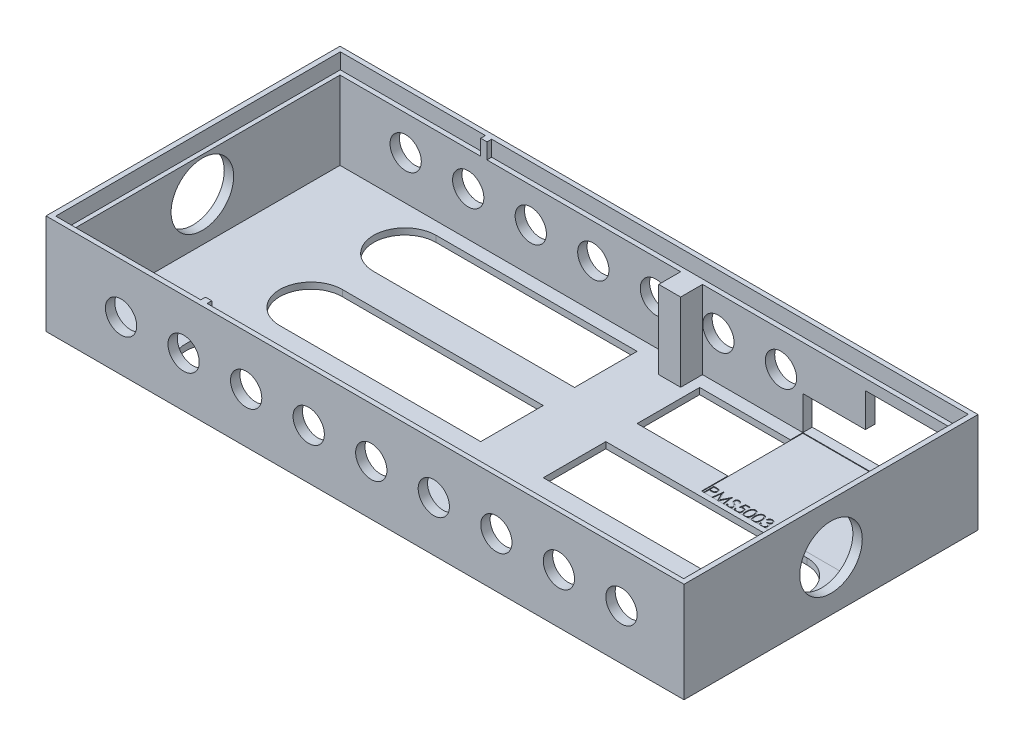
SolidWorks part; units mm, degrees
ref_plane "Alzado" through (0, 0, 0) normal (0, 0, 1) x (1, 0, 0)
ref_plane "Planta" through (0, 0, 0) normal (0, 1, 0) x (1, 0, 0)
ref_plane "Vista lateral" through (0, 0, 0) normal (1, 0, 0) x (0, 0, -1)
sketch "Croquis1" plane through (0, 0, 0) normal (0, 1, 0) x (1, 0, 0)
  line L1 (101, 46.5) -> (-101, 46.5)
  line L2 (101, 46.5) -> (101, -46.5)
  line L3 (101, -46.5) -> (-101, -46.5)
  line L4 (-101, 46.5) -> (-101, -46.5)
  line L5 (101, 46.5) -> (-101, -46.5) construction
  line L6 (101, -46.5) -> (-101, 46.5) construction
  line L7 (99, 44) -> (-99, 44)
  line L8 (99, 44) -> (99, -44)
  line L9 (99, -44) -> (-99, -44)
  line L10 (-99, 44) -> (-99, -44)
  line L11 (99, 44) -> (-99, -44) construction
  line L12 (99, -44) -> (-99, 44) construction
  point P0 (0, 0)
  point P6 (0, 0)
extrude "Saliente-Extruir2" add sketch "Croquis1" along normal blind 25
sketch "Croquis3" plane through (0, 0, 0) normal (0, -1, 0) x (1, 0, 0)
  line L1 (-101, -46.5) -> (101, -46.5)
  line L2 (-101, -46.5) -> (-101, 46.5)
  line L3 (-101, 46.5) -> (101, 46.5)
  line L4 (101, -46.5) -> (101, 46.5)
extrude "Saliente-Extruir3" add sketch "Croquis3" along normal blind 2
sketch "Croquis4" plane through (0, 25, 0) normal (0, 1, 0) x (1, 0, 0)
  line L1 (99, 44) -> (99, -44)
  line L2 (101, 46.5) -> (101, -46.5)
  line L4 (102, 47) -> (-102, 47)
  line L5 (102, 47) -> (102, -47)
  line L6 (102, -47) -> (-102, -47)
  line L7 (-102, 47) -> (-102, -47)
  line L8 (102, 47) -> (-102, -47) construction
  line L9 (102, -47) -> (-102, 47) construction
  line L10 (101, 46.5) -> (-101, 46.5)
  line L11 (101, 46.5) -> (101, -46.5)
  line L12 (101, -46.5) -> (-101, -46.5)
  line L13 (-101, 46.5) -> (-101, -46.5)
  line L14 (101, 46.5) -> (-101, -46.5) construction
  line L15 (101, -46.5) -> (-101, 46.5) construction
  point P8 (0, 0)
  point P14 (0, 0)
  line M10 (-101, 46.5) -> (-101, -46.5)
  line M11 (-101, -46.5) -> (101, -46.5)
  line M12 (101, -46.5) -> (101, 46.5)
  line M13 (101, 46.5) -> (-101, 46.5)
extrude "Saliente-Extruir5" add sketch "Croquis4" against normal up to surface (27 mm away) contours L4 L7 L6 L5 M10 M13 M12 M11 up to face at (0, -2, 0)
sketch "Croquis5" plane through (0, 25, 0) normal (0, 1, 0) x (1, 0, 0)
  line L0 (-99, 44) -> (-99, -44)
  line L1 (-102, -47) -> (-102, 47)
  line L3 (102, 47) -> (-102, 47)
  line L4 (102, 47) -> (102, -47)
  line L5 (102, -47) -> (-102, -47)
  line L6 (-102, 47) -> (-102, -47)
  line L7 (102, 47) -> (-102, -47) construction
  line L8 (102, -47) -> (-102, 47) construction
  line L9 (100.3948, 45.5) -> (-100.3948, 45.5)
  line L10 (100.3948, 45.5) -> (100.3948, -45.5)
  line L11 (100.3948, -45.5) -> (-100.3948, -45.5)
  line L12 (-100.3948, 45.5) -> (-100.3948, -45.5)
  line L13 (100.3948, 45.5) -> (-100.3948, -45.5) construction
  line L14 (100.3948, -45.5) -> (-100.3948, 45.5) construction
  point P8 (0, 0)
  point P9 (0, 0)
  line M15 (102, 47) -> (-102, 47)
  line M16 (-102, 47) -> (-102, -47)
  line M17 (-102, -47) -> (102, -47)
  line M18 (102, -47) -> (102, 47)
extrude "Saliente-Extruir6" add sketch "Croquis5" along normal blind 5 contours L12 L9 L10 L11 M18 M15 M16 M17
sketch "Croquis6" plane through (0, 25, 0) normal (0, 1, 0) x (1, 0, 0)
  line L1 (100.3948, 45.5) -> (-52.0021, 45.5)
  line L2 (100.3948, 45.5) -> (-100.3948, 45.5) construction
  line L3 (99, 44) -> (-99, 44) construction
  line L6 (-52.0021, -45.5) -> (-100.3948, -45.5)
  line L7 (-100.3948, 45.5) -> (-100.3948, -45.5)
  line L12 (-52.0021, 44) -> (-54.0021, 44)
  line L13 (-52.0021, 44) -> (-52.0021, 45.5)
  line L14 (-52.0021, 45.5) -> (-54.0021, 45.5)
  line L15 (-54.0021, 44) -> (-54.0021, 45.5)
  line L16 (-99, -44) -> (99, -44) construction
  line L17 (-52.0021, -45.5) -> (-54.0021, -45.5)
  line L18 (-52.0021, -45.5) -> (-52.0021, -44)
  line L19 (-52.0021, -44) -> (-54.0021, -44)
  line L20 (-54.0021, -45.5) -> (-54.0021, -44)
  line M7 (100.3948, 45.5) -> (-100.3948, 45.5)
  line M12 (-99, 44) -> (99, 44)
  line M14 (99, -44) -> (-99, -44)
extrude "Saliente-Extruir7" add sketch "Croquis6" along normal blind 5 contours L20 L6 L18 M14 | L15 L13 M12 M7
sketch "Croquis7" plane through (0, 25, 0) normal (0, 1, 0) x (1, 0, 0)
  line L0 (100.3948, 45.5) -> (-52.0021, 45.5)
sketch "Croquis8" plane through (0, 0, 0) normal (0, 1, 0) x (1, 0, 0)
  line L0 (0, 0) -> (-99, 0)
  line L1 (-99, 44) -> (-99, -44) construction
  line L2 (-49.5, 0) -> (-99, 0)
  line L3 (0, 0) -> (0, 44)
  line L8 (99, 44) -> (-99, 44) construction
  line L9 (74.25, -10) -> (0, 0) construction
  line L10 (84.25, -10) -> (-64.25, -10)
  line L11 (84.25, 10) -> (-64.25, 10)
  line L12 (84.25, 20) -> (-64.25, 20)
  line L13 (84.25, 40) -> (-64.25, 40)
  line L16 (84.25, -40) -> (-64.25, -40)
  line L17 (84.25, -20) -> (-64.25, -20)
  arc A2 (-64.25, 10) -> (-64.25, -10) centre (-64.25, 0) ccw
  arc A3 (84.25, -10) -> (84.25, 10) centre (84.25, 0) ccw
  arc A4 (-64.25, 40) -> (-64.25, 20) centre (-64.25, 30) ccw
  arc A5 (84.25, 20) -> (84.25, 40) centre (84.25, 30) ccw
  arc A8 (-64.25, -20) -> (-64.25, -40) centre (-64.25, -30) ccw
  arc A9 (84.25, -40) -> (84.25, -20) centre (84.25, -30) ccw
  dimension "D1" = 2
extrude "Cortar-Extruir1" cut sketch "Croquis8" against normal blind 5 contours L10 A2 L11 A3 | L12 A4 L13 A5 | L16 A8 L17 A9
sketch "Croquis9" plane through (0, 0, -44) normal (0, 0, 1) x (1, 0, 0)
  line L0 (99, 0) -> (69, 0)
  line L1 (99, 0) -> (-99, 0) construction
  line L2 (69, 1.6237) -> (69, 21.6237)
  line L4 (69, 21.6237) -> (99, 21.6237)
  line L5 (69, 21.6237) -> (69, 0)
  line L6 (69, 0) -> (99, 0)
  line L7 (99, 21.6237) -> (99, 0)
  line M2 (-99, 0) -> (99, 0)
  line M3 (99, 0) -> (99, 25)
extrude "Cortar-Extruir2" cut sketch "Croquis9" against normal blind 25 contours L2 L5 L4 M2 M3
sketch "Croquis10" plane through (0, 0, -44) normal (0, 0, 1) x (1, 0, 0)
  line L0 (69, 0) -> (49, 0)
  line L1 (69, 0) -> (-99, 0) construction
  line L2 (49, 0) -> (69, 21.6237)
  line L3 (69, 21.6237) -> (69, 0)
  line L5 (49, 0) -> (69, 0)
  line L6 (49, 0) -> (49, 10.8118)
  line L7 (49, 10.8118) -> (69, 10.8118)
  line L8 (69, 0) -> (69, 10.8118)
  line M1 (-99, 0) -> (69, 0)
  line M2 (69, 0) -> (69, 21.6237)
extrude "Cortar-Extruir3" cut sketch "Croquis10" against normal blind 25 contours L7 L6 L2 | L7 L2 M1 M2
sketch "Croquis11" plane through (0, 0, 47) normal (0, 0, 1) x (1, 0, 0)
  line L0 (102, 14) -> (82, 14)
  line L1 (102, -2) -> (102, 30) construction
  circle A0 centre (82, 14) radius 5
  circle A1 centre (62, 14) radius 5
  circle A2 centre (42, 14) radius 5
  circle A3 centre (22, 14) radius 5
  circle A4 centre (2, 14) radius 5
  circle A5 centre (-18, 14) radius 5
  circle A6 centre (-38, 14) radius 5
  circle A7 centre (-58, 14) radius 5
  circle A8 centre (-78, 14) radius 5
  dimension "D1" = 9
extrude "Cortar-Extruir4" cut sketch "Croquis11" against normal blind 100
sketch "Croquis12" plane through (0, 0, -44) normal (0, 0, 1) x (1, 0, 0)
  line L1 (69, 10.8118) -> (53.1179, 10.8118)
  line L2 (69, 10.8118) -> (69, 21.4227)
  line L3 (69, 21.4227) -> (53.1179, 21.4227)
  line L4 (53.1179, 10.8118) -> (53.1179, 21.4227)
extrude "Saliente-Extruir9" add sketch "Croquis12" against normal up to surface (3 mm away) up to face at (-83, 14, -47)
sketch "Croquis13" plane through (0, 0, 0) normal (0, 1, 0) x (1, 0, 0)
  line L0 (-74.25, 0) -> (94.25, 0)
  line L1 (84.25, 40) -> (-64.25, 40) construction
  line L2 (20, -40) -> (0, -40)
  line L3 (20, -40) -> (20, 40)
  line L4 (20, 40) -> (0, 40)
  line L5 (0, -40) -> (0, 40)
  line L6 (20, -40) -> (0, 40) construction
  line L7 (20, 40) -> (0, -40) construction
  arc A0 (-64.25, 10) -> (-64.25, -10) centre (-64.25, 0) ccw construction
  arc A1 (84.25, -10) -> (84.25, 10) centre (84.25, 0) ccw construction
  point P8 (10, 0)
  line M12 (84.25, -10) -> (-64.25, -10)
  line M14 (-64.25, 10) -> (84.25, 10)
  line M16 (84.25, -40) -> (-64.25, -40)
  line M18 (-64.25, -20) -> (84.25, -20)
  line M20 (84.25, 20) -> (-64.25, 20)
  line M22 (-64.25, 40) -> (84.25, 40)
extrude "Saliente-Extruir10" add sketch "Croquis13" against normal up to surface (2 mm away) contours L5 L3 M16 M18 | L5 L3 L0 M12 | L5 L0 L3 M14 | L5 L3 M20 M22 up to face at (10, -2, 30)
sketch "Croquis14" plane through (0, 0, 0) normal (0, 1, 0) x (1, 0, 0)
  line L0 (99, -44) -> (99, 47) construction
  line L1 (49, 44) -> (99, 44)
  line L2 (49, 44) -> (49, 16.4431)
  line L3 (49, 16.4431) -> (99, 16.4431)
  line L4 (99, 44) -> (99, 16.4431)
extrude "Saliente-Extruir11" add sketch "Croquis14" against normal up to surface (2 mm away)
sketch "Croquis15" plane through (102, 0, 0) normal (1, 0, 0) x (0, 0, -1)
  line L0 (-47, 14) -> (47, 14)
  line L1 (-47, -2) -> (-47, 30) construction
  line L2 (47, -2) -> (47, 30) construction
  circle A0 centre (0, 14) radius 10
extrude "Cortar-Extruir5" cut sketch "Croquis15" against normal blind 257 contours L0 A0 | L0 A0
sketch "Croquis16" plane through (0, 0, 0) normal (0, 1, 0) x (1, 0, 0)
  line L0 (49, 44) -> (-99, 44) construction
  line L1 (16.915, 44) -> (9.915, 44)
  line L2 (16.915, 44) -> (16.915, 37)
  line L3 (16.915, 37) -> (9.915, 37)
  line L4 (9.915, 44) -> (9.915, 37)
extrude "Saliente-Extruir12" add sketch "Croquis16" along normal up to vertex
sketch "Croquis17" plane through (0, 0, 0) normal (0, 1, 0) x (1, 0, 0)
  line L1 (99, -44) -> (98, -44)
  line L2 (99, -44) -> (99, -43)
  line L3 (99, -43) -> (98, -43)
  line L4 (98, -44) -> (98, -43)
extrude "Saliente-Extruir13" add sketch "Croquis17" along normal up to vertex
sketch "Croquis18" plane through (0, 0, 0) normal (0, 1, 0) x (1, 0, 0)
  line L0 (99, -43) -> (99, 47) construction
  line L1 (49, 44) -> (99, 44)
  line L2 (49, 44) -> (49, 11.5953)
  line L3 (49, 11.5953) -> (99, 11.5953)
  line L4 (99, 44) -> (99, 11.5953)
extrude "Cortar-Extruir6" cut sketch "Croquis18" against normal blind 0.2
sketch "Croquis19" plane through (0, -0.2, 0) normal (0, 1, 0) x (1, 0, 0)
  text T0 "PMS5003"
extrude "Cortar-Extruir7" cut sketch "Croquis19" against normal blind 0.2
